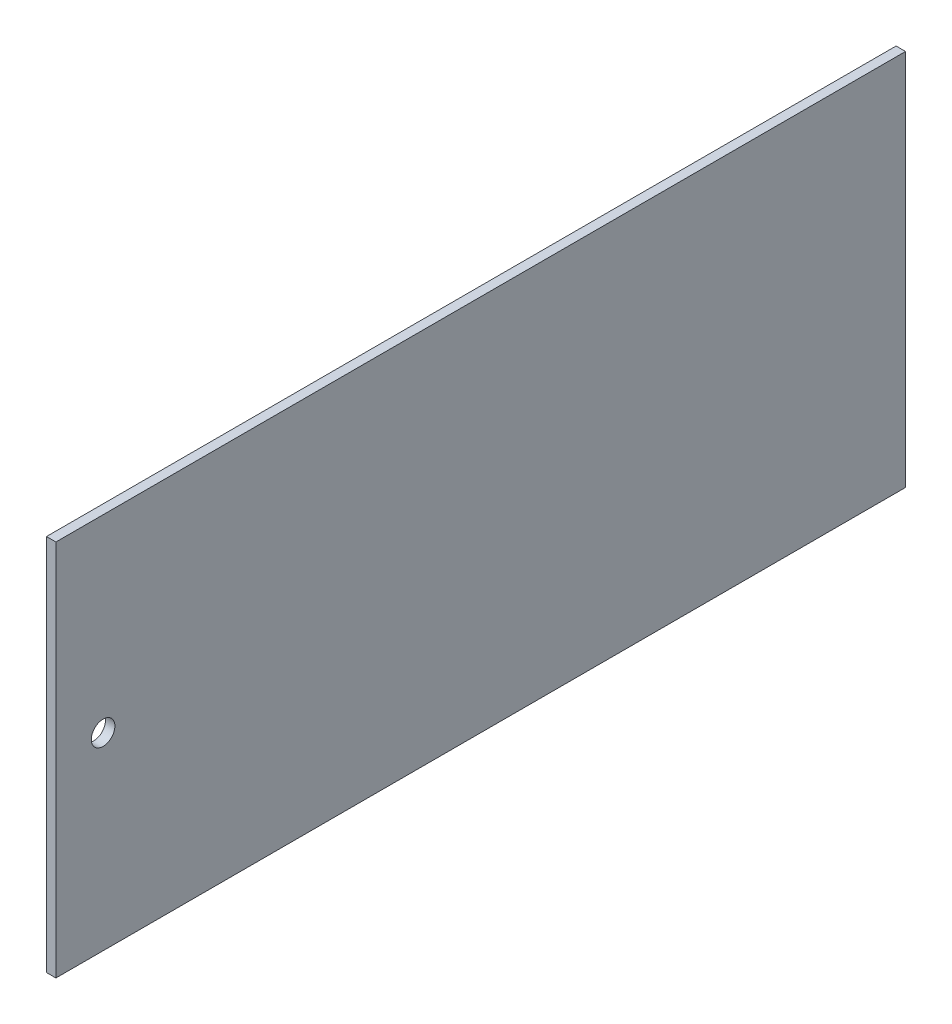
SolidWorks part; units mm, degrees
ref_plane "Front Plane" through (0, 0, 0) normal (0, 0, 1) x (1, 0, 0)
ref_plane "Top Plane" through (0, 0, 0) normal (0, 1, 0) x (1, 0, 0)
ref_plane "Right Plane" through (0, 0, 0) normal (1, 0, 0) x (0, 0, -1)
sketch "Sketch1" plane through (0, 0, 0) normal (1, 0, 0) x (0, 0, -1)
  line L1 (-114.3, -50.8) -> (114.3, -50.8)
  line L2 (-114.3, -50.8) -> (-114.3, 50.8)
  line L3 (-114.3, 50.8) -> (114.3, 50.8)
  line L4 (114.3, -50.8) -> (114.3, 50.8)
  line L5 (-114.3, -50.8) -> (114.3, 50.8) construction
  line L6 (-114.3, 50.8) -> (114.3, -50.8) construction
  point P0 (0, 0)
  dimension "D1" = 228.6
  dimension "D2" = 101.6
extrude "Boss-Extrude1" add sketch "Sketch1" against normal blind 2.54
sketch "Sketch2" plane through (0, 0, 0) normal (1, 0, 0) x (0, 0, -1)
  line L0 (-114.3, 50.8) -> (-114.3, -50.8) construction
  circle A0 centre (-101.6, 0) radius 3.175
  dimension "D1" = 6.35
  dimension "D2" = 12.7
extrude "Cut-Extrude1" cut sketch "Sketch2" against normal up to next contours A0
